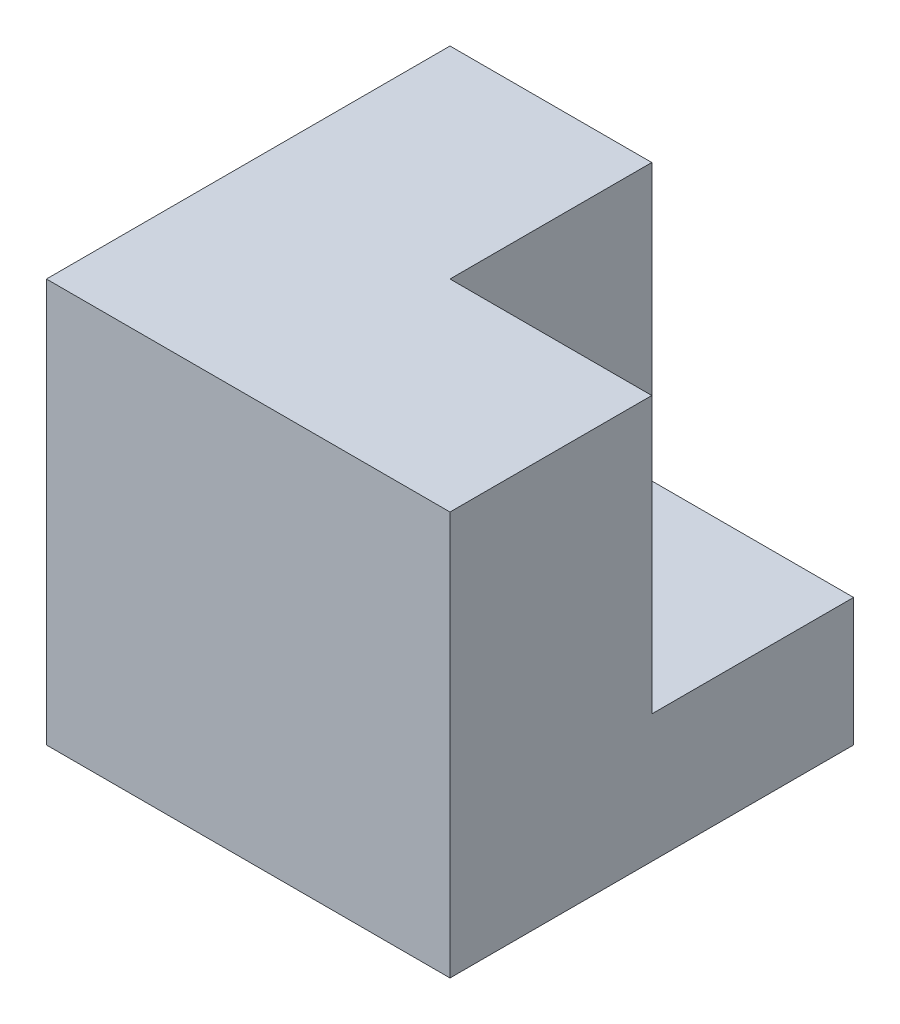
SolidWorks part; units mm, degrees
ref_plane "Front Plane" through (0, 0, 0) normal (0, 0, 1) x (1, 0, 0)
ref_plane "Top Plane" through (0, 0, 0) normal (0, 1, 0) x (1, 0, 0)
ref_plane "Right Plane" through (0, 0, 0) normal (1, 0, 0) x (0, 0, -1)
sketch "Sketch1" plane through (0, 0, 0) normal (0, 0, 1) x (1, 0, 0)
  line L1 (0, 0) -> (76.2, 0)
  line L2 (0, 0) -> (0, 76.2)
  line L3 (0, 76.2) -> (76.2, 76.2)
  line L4 (76.2, 0) -> (76.2, 76.2)
  dimension "D1" = 76.2
extrude "Boss-Extrude1" add sketch "Sketch1" along normal blind 76.2
sketch "Sketch2" plane through (76.2, 0, 0) normal (1, 0, 0) x (0, 0, -1)
  line L0 (-76.2, 0) -> (0, 0) construction
  line L1 (0, 76.2) -> (-38.1, 76.2)
  line L2 (0, 76.2) -> (0, 24.13)
  line L3 (0, 24.13) -> (-38.1, 24.13)
  line L4 (-38.1, 76.2) -> (-38.1, 24.13)
  dimension "D1" = 24.13
  dimension "D2" = 38.1
extrude "Cut-Extrude1" cut sketch "Sketch2" against normal blind 38.1
